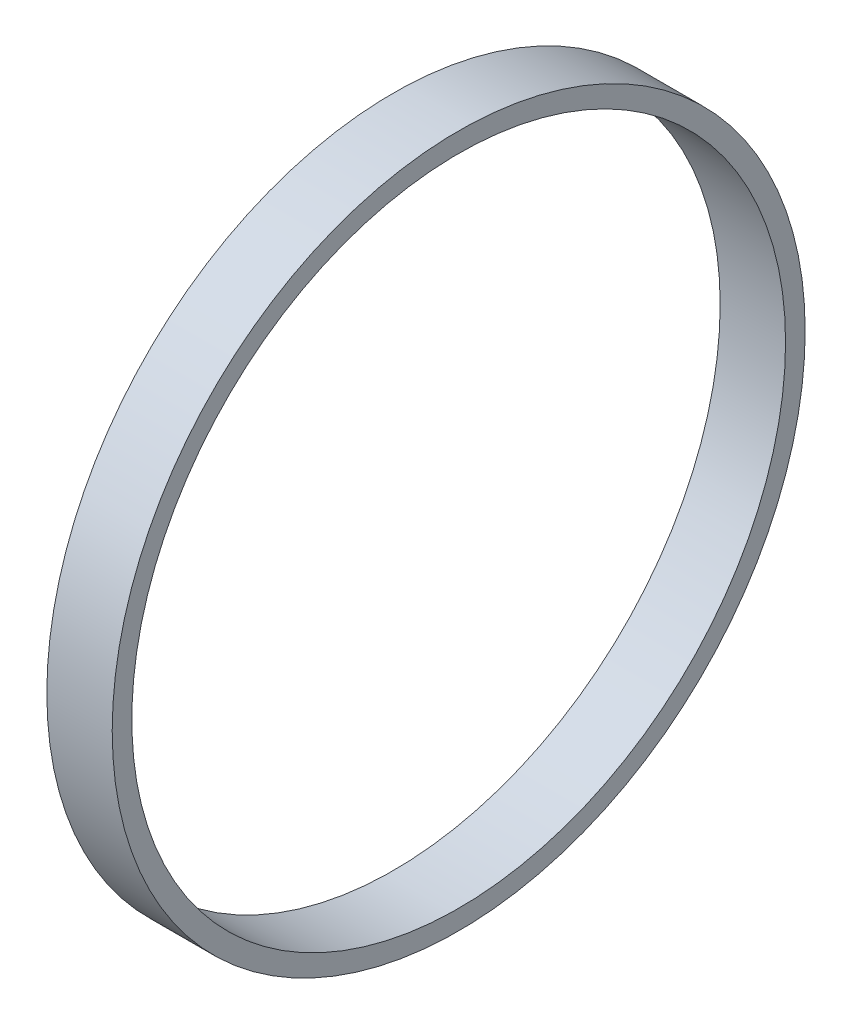
SolidWorks part; units mm, degrees
ref_plane "Front Plane" through (0, 0, 0) normal (0, 0, 1) x (1, 0, 0)
ref_plane "Top Plane" through (0, 0, 0) normal (0, 1, 0) x (1, 0, 0)
ref_plane "Right Plane" through (0, 0, 0) normal (1, 0, 0) x (0, 0, -1)
sketch "Sketch1" plane through (0, 0, 0) normal (1, 0, 0) x (0, 0, -1)
  circle A0 centre (0, 0) radius 25
  circle A1 centre (0, 0) radius 26.5
  dimension "D1" = 1.5
extrude "Boss-Extrude1" add sketch "Sketch1" along normal blind 5
